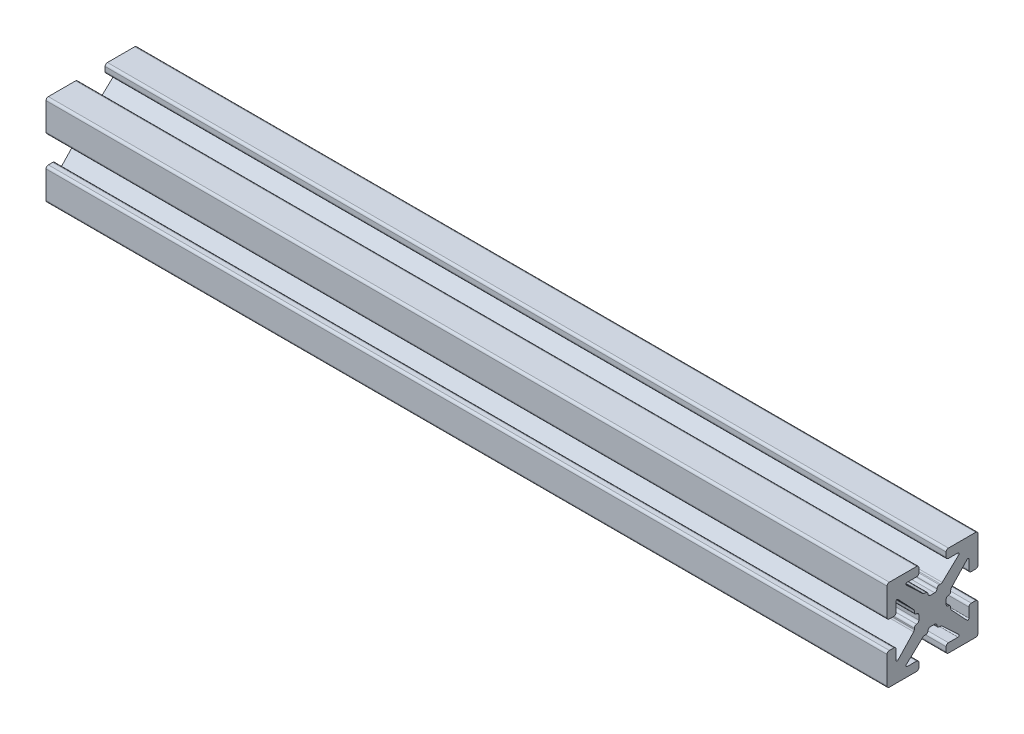
SolidWorks part; units mm, degrees
ref_plane "Front Plane" through (0, 0, 0) normal (0, 0, 1) x (1, 0, 0)
ref_plane "Top Plane" through (0, 0, 0) normal (0, 1, 0) x (1, 0, 0)
ref_plane "Right Plane" through (0, 0, 0) normal (1, 0, 0) x (0, 0, -1)
sketch "Sketch1" plane through (0, 0, 0) normal (1, 0, 0) x (0, 0, -1)
  line L0 (0, 0) -> (0, 1.4986) construction
  line L1 (-0.2413, 1.4986) -> (0.2413, 1.4986)
  line L2 (5.0038, 1.7526) -> (5.0038, 4.7498)
  line L3 (0.7493, 2.0066) -> (0.8899, 2.0066)
  line L4 (1.0639, 2.0756) -> (2.8908, 3.7937)
  line L5 (2.8038, 4.0132) -> (1.7526, 4.0132)
  line L6 (1.4986, 4.2672) -> (1.4986, 4.7498)
  line L7 (1.7526, 5.0038) -> (4.7498, 5.0038)
  line L8 (5.0038, 5.0038) -> (0, 0) construction
  line L9 (0, 0) -> (8.6271, 0) construction
  line L10 (0, 0) -> (0, 5.0038) construction
  line L11 (4.2672, 1.4986) -> (4.7498, 1.4986)
  line L12 (4.0132, 2.8038) -> (4.0132, 1.7526)
  line L13 (2.0756, 1.0639) -> (3.7937, 2.8908)
  line L14 (2.0066, 0.7493) -> (2.0066, 0.8899)
  line L15 (1.4986, -0.2413) -> (1.4986, 0.2413)
  line L16 (0, 0) -> (1.4986, 0) construction
  line L17 (-0.2413, -1.4986) -> (0.2413, -1.4986)
  line L18 (0.7493, -2.0066) -> (0.8899, -2.0066)
  line L19 (1.0639, -2.0756) -> (2.8908, -3.7937)
  line L20 (2.8038, -4.0132) -> (1.7526, -4.0132)
  line L21 (1.4986, -4.2672) -> (1.4986, -4.7498)
  line L22 (1.7526, -5.0038) -> (4.7498, -5.0038)
  line L23 (5.0038, -1.7526) -> (5.0038, -4.7498)
  line L24 (4.2672, -1.4986) -> (4.7498, -1.4986)
  line L25 (4.0132, -2.8038) -> (4.0132, -1.7526)
  line L26 (2.0756, -1.0639) -> (3.7937, -2.8908)
  line L27 (2.0066, -0.7493) -> (2.0066, -0.8899)
  line L28 (-0.7493, 2.0066) -> (-0.8899, 2.0066)
  line L29 (-1.0639, 2.0756) -> (-2.8908, 3.7937)
  line L30 (-2.8038, 4.0132) -> (-1.7526, 4.0132)
  line L31 (-1.4986, 4.2672) -> (-1.4986, 4.7498)
  line L32 (-1.7526, 5.0038) -> (-4.7498, 5.0038)
  line L33 (-5.0038, 1.7526) -> (-5.0038, 4.7498)
  line L34 (-4.2672, 1.4986) -> (-4.7498, 1.4986)
  line L35 (-4.0132, 2.8038) -> (-4.0132, 1.7526)
  line L36 (-2.0756, 1.0639) -> (-3.7937, 2.8908)
  line L37 (-2.0066, 0.7493) -> (-2.0066, 0.8899)
  line L38 (-1.4986, -0.2413) -> (-1.4986, 0.2413)
  line L39 (-2.0066, -0.7493) -> (-2.0066, -0.8899)
  line L40 (-2.0756, -1.0639) -> (-3.7937, -2.8908)
  line L41 (-4.0132, -2.8038) -> (-4.0132, -1.7526)
  line L42 (-4.2672, -1.4986) -> (-4.7498, -1.4986)
  line L43 (-5.0038, -1.7526) -> (-5.0038, -4.7498)
  line L44 (-1.7526, -5.0038) -> (-4.7498, -5.0038)
  line L45 (-1.4986, -4.2672) -> (-1.4986, -4.7498)
  line L46 (-2.8038, -4.0132) -> (-1.7526, -4.0132)
  line L47 (-1.0639, -2.0756) -> (-2.8908, -3.7937)
  line L48 (-0.7493, -2.0066) -> (-0.8899, -2.0066)
  arc A0 (2.8908, 3.7937) -> (2.8038, 4.0132) centre (2.8038, 3.8862) ccw
  arc A1 (0.4953, 1.7526) -> (0.7493, 2.0066) centre (0.7493, 1.7526) cw
  arc A2 (0.8899, 2.0066) -> (1.0639, 2.0756) centre (0.8899, 2.2606) ccw
  arc A3 (1.7526, 4.0132) -> (1.4986, 4.2672) centre (1.7526, 4.2672) cw
  arc A4 (1.4986, 4.7498) -> (1.7526, 5.0038) centre (1.7526, 4.7498) cw
  arc A5 (0.2413, 1.4986) -> (0.4953, 1.7526) centre (0.2413, 1.7526) ccw
  arc A6 (4.7498, 1.4986) -> (5.0038, 1.7526) centre (4.7498, 1.7526) ccw
  arc A7 (4.0132, 1.7526) -> (4.2672, 1.4986) centre (4.2672, 1.7526) ccw
  arc A8 (3.7937, 2.8908) -> (4.0132, 2.8038) centre (3.8862, 2.8038) cw
  arc A9 (2.0066, 0.8899) -> (2.0756, 1.0639) centre (2.2606, 0.8899) cw
  arc A10 (1.7526, 0.4953) -> (2.0066, 0.7493) centre (1.7526, 0.7493) ccw
  arc A11 (1.4986, 0.2413) -> (1.7526, 0.4953) centre (1.7526, 0.2413) cw
  arc A12 (0.2413, -1.4986) -> (0.4953, -1.7526) centre (0.2413, -1.7526) cw
  arc A13 (0.4953, -1.7526) -> (0.7493, -2.0066) centre (0.7493, -1.7526) ccw
  arc A14 (0.8899, -2.0066) -> (1.0639, -2.0756) centre (0.8899, -2.2606) cw
  arc A15 (2.8908, -3.7937) -> (2.8038, -4.0132) centre (2.8038, -3.8862) cw
  arc A16 (1.7526, -4.0132) -> (1.4986, -4.2672) centre (1.7526, -4.2672) ccw
  arc A17 (1.4986, -4.7498) -> (1.7526, -5.0038) centre (1.7526, -4.7498) ccw
  arc A18 (4.7498, -1.4986) -> (5.0038, -1.7526) centre (4.7498, -1.7526) cw
  arc A19 (4.0132, -1.7526) -> (4.2672, -1.4986) centre (4.2672, -1.7526) cw
  arc A20 (3.7937, -2.8908) -> (4.0132, -2.8038) centre (3.8862, -2.8038) ccw
  arc A21 (2.0066, -0.8899) -> (2.0756, -1.0639) centre (2.2606, -0.8899) ccw
  arc A22 (1.7526, -0.4953) -> (2.0066, -0.7493) centre (1.7526, -0.7493) cw
  arc A23 (1.4986, -0.2413) -> (1.7526, -0.4953) centre (1.7526, -0.2413) ccw
  arc A24 (-0.2413, 1.4986) -> (-0.4953, 1.7526) centre (-0.2413, 1.7526) cw
  arc A25 (-0.4953, 1.7526) -> (-0.7493, 2.0066) centre (-0.7493, 1.7526) ccw
  arc A26 (-0.8899, 2.0066) -> (-1.0639, 2.0756) centre (-0.8899, 2.2606) cw
  arc A27 (-2.8908, 3.7937) -> (-2.8038, 4.0132) centre (-2.8038, 3.8862) cw
  arc A28 (-1.7526, 4.0132) -> (-1.4986, 4.2672) centre (-1.7526, 4.2672) ccw
  arc A29 (-1.4986, 4.7498) -> (-1.7526, 5.0038) centre (-1.7526, 4.7498) ccw
  arc A30 (-4.7498, 1.4986) -> (-5.0038, 1.7526) centre (-4.7498, 1.7526) cw
  arc A31 (-4.0132, 1.7526) -> (-4.2672, 1.4986) centre (-4.2672, 1.7526) cw
  arc A32 (-3.7937, 2.8908) -> (-4.0132, 2.8038) centre (-3.8862, 2.8038) ccw
  arc A33 (-2.0066, 0.8899) -> (-2.0756, 1.0639) centre (-2.2606, 0.8899) ccw
  arc A34 (-1.7526, 0.4953) -> (-2.0066, 0.7493) centre (-1.7526, 0.7493) cw
  arc A35 (-1.4986, 0.2413) -> (-1.7526, 0.4953) centre (-1.7526, 0.2413) ccw
  arc A36 (-1.4986, -0.2413) -> (-1.7526, -0.4953) centre (-1.7526, -0.2413) cw
  arc A37 (-1.7526, -0.4953) -> (-2.0066, -0.7493) centre (-1.7526, -0.7493) ccw
  arc A38 (-2.0066, -0.8899) -> (-2.0756, -1.0639) centre (-2.2606, -0.8899) cw
  arc A39 (-3.7937, -2.8908) -> (-4.0132, -2.8038) centre (-3.8862, -2.8038) cw
  arc A40 (-4.0132, -1.7526) -> (-4.2672, -1.4986) centre (-4.2672, -1.7526) ccw
  arc A41 (-4.7498, -1.4986) -> (-5.0038, -1.7526) centre (-4.7498, -1.7526) ccw
  arc A42 (-1.4986, -4.7498) -> (-1.7526, -5.0038) centre (-1.7526, -4.7498) cw
  arc A43 (-1.7526, -4.0132) -> (-1.4986, -4.2672) centre (-1.7526, -4.2672) cw
  arc A44 (-2.8908, -3.7937) -> (-2.8038, -4.0132) centre (-2.8038, -3.8862) ccw
  arc A45 (-0.8899, -2.0066) -> (-1.0639, -2.0756) centre (-0.8899, -2.2606) ccw
  arc A46 (-0.4953, -1.7526) -> (-0.7493, -2.0066) centre (-0.7493, -1.7526) cw
  arc A47 (-0.2413, -1.4986) -> (-0.4953, -1.7526) centre (-0.2413, -1.7526) ccw
  arc A48 (-4.7498, 5.0038) -> (-5.0038, 4.7498) centre (-4.7498, 4.7498) ccw
  arc A49 (-5.0038, -4.7498) -> (-4.7498, -5.0038) centre (-4.7498, -4.7498) ccw
  arc A50 (4.7498, -5.0038) -> (5.0038, -4.7498) centre (4.7498, -4.7498) ccw
  arc A51 (4.7498, 5.0038) -> (5.0038, 4.7498) centre (4.7498, 4.7498) cw
  point P14 (3.1242, 4.0132)
  point P19 (0.9906, 2.0066)
  point P150 (0, -1.4986)
  point P152 (-5.0038, 5.0038)
  point P155 (-5.0038, -5.0038)
  point P158 (5.0038, -5.0038)
  dimension "D10" = 0.127
  dimension "D11" = 0.254
  dimension "D2" = 0.254
  dimension "D1" = 10.0076
  dimension "D3" = 2.9972
  dimension "D4" = 0.508
  dimension "D5" = 2.9972
  dimension "D6" = 0.9906
  dimension "D7" = 1.6256
  dimension "D8" = 1.9812
  dimension "D9" = 0.9906
extrude "Boss.-Extru.1" add sketch "Sketch1" along normal blind 92.5
